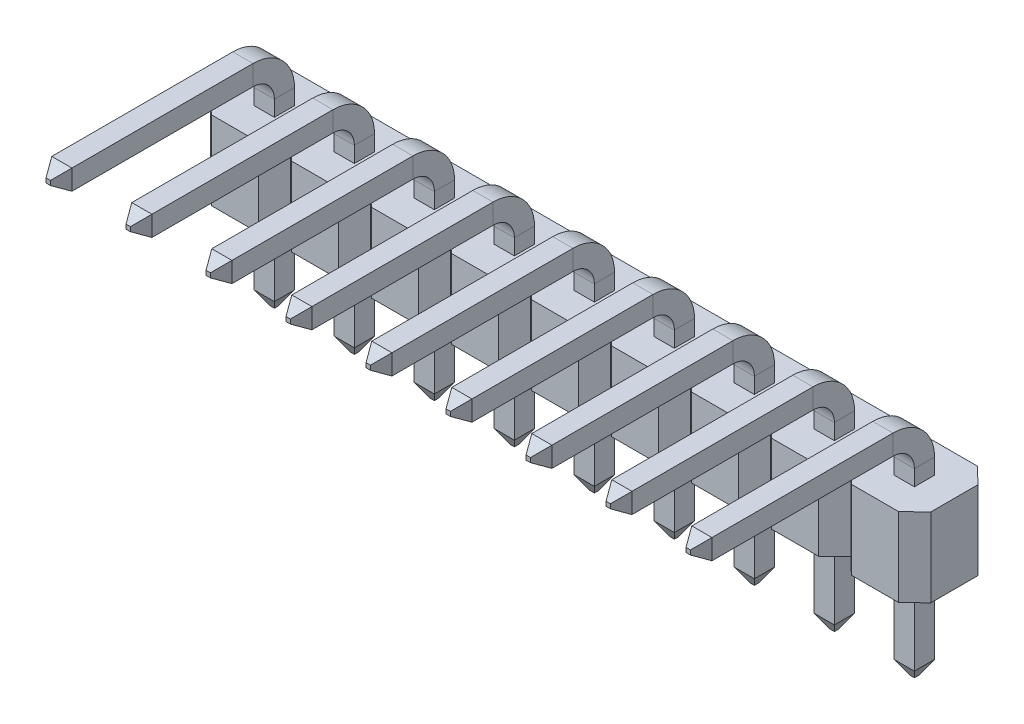
SolidWorks part; units mm, degrees
other "Plastic Body"
other "Metal Pin"
material "ABS"
ref_plane "Front Plane" through (0, 0, 0) normal (0, 0, 1) x (1, 0, 0)
ref_plane "Top Plane" through (0, 0, 0) normal (0, 1, 0) x (1, 0, 0)
ref_plane "Right Plane" through (0, 0, 0) normal (1, 0, 0) x (0, 0, -1)
sketch "Sketch1" plane through (0, 0, 0) normal (0, 1, 0) x (1, 0, 0)
  line L0 (0, 1.25) -> (0, -1.25) construction
  line L1 (-1.27, 1.25) -> (1.27, 1.25)
  line L2 (-1.27, 1.25) -> (-1.27, -1.25)
  line L3 (-1.27, -1.25) -> (1.27, -1.25)
  line L4 (1.27, 1.25) -> (1.27, -1.25)
  line L6 (-0.32, 0.32) -> (0.32, 0.32)
  line L7 (-0.32, 0.32) -> (-0.32, -0.32)
  line L8 (-0.32, -0.32) -> (0.32, -0.32)
  line L9 (0.32, 0.32) -> (0.32, -0.32)
  line L10 (-0.32, 0.32) -> (0.32, -0.32) construction
  line L11 (-0.32, -0.32) -> (0.32, 0.32) construction
  point P7 (0, 0)
  dimension "D1" = 2.5
  dimension "D2" = 2.54
  dimension "D3" = 0.64
extrude "Plastic Connection Body" add sketch "Sketch1" along normal blind 2.5
sketch "Sketch3" plane through (0, 2.5, 0) normal (0, 1, 0) x (1, 0, 0)
  line L5 (0, 1.25) -> (0, -1.25) construction
  line L6 (1.27, 1.25) -> (-1.27, 1.25) construction
  line L7 (-1.27, 0) -> (1.27, 0) construction
  line L8 (-1.27, 1.25) -> (-1.27, -1.25) construction
  line L9 (-0.75, 1.25) -> (0.75, 1.25) construction
  line L10 (-0.75, -1.25) -> (0.75, -1.25) construction
  line L11 (-1.27, 0.75) -> (-1.27, -0.75) construction
  line L12 (1.27, 0.75) -> (1.27, -0.75) construction
  line L13 (-0.75, 1.25) -> (-1.27, 0.75)
  line L14 (-1.27, 0.75) -> (-1.27, 1.25)
  line L15 (-1.27, 1.25) -> (-0.75, 1.25)
  line L16 (0.75, 1.25) -> (1.27, 0.75)
  line L17 (1.27, 0.75) -> (1.27, 1.25)
  line L18 (1.27, 1.25) -> (0.75, 1.25)
  line L19 (-1.27, -0.75) -> (-1.27, -1.25)
  line L20 (-1.27, -1.25) -> (-0.75, -1.25)
  line L21 (-0.75, -1.25) -> (-1.27, -0.75)
  line L22 (0.75, -1.25) -> (1.27, -0.75)
  line L23 (1.27, -0.75) -> (1.27, -1.25)
  line L24 (1.27, -1.25) -> (0.75, -1.25)
  dimension "D1" = 1.5
extrude "Corners Trimmed" cut sketch "Sketch3" against normal up to surface (2.5 mm away) up to face at (0, 0, 0)
sketch "Sketch4" plane through (0, 0, 0) normal (0, -1, 0) x (1, 0, 0)
  line L0 (-0.32, -0.32) -> (-0.32, 0.32) construction
  line L1 (-0.32, 0.32) -> (0.32, 0.32) construction
  line L2 (0.32, 0.32) -> (0.32, -0.32) construction
  line L3 (0.32, -0.32) -> (-0.32, -0.32) construction
  line L4 (-0.32, -0.32) -> (-0.32, 0.32)
  line L5 (-0.32, 0.32) -> (0.32, 0.32)
  line L6 (0.32, 0.32) -> (0.32, -0.32)
  line L7 (0.32, -0.32) -> (-0.32, -0.32)
sketch "Sketch5" plane through (0, 0, 0) normal (1, 0, 0) x (0, 0, -1)
  line L0 (0, 3) -> (0, -3)
  line L1 (-1, 4) -> (-7.18, 4)
  arc A0 (0, 3) -> (-1, 4) centre (-1, 3) ccw
  dimension "D4" = 1
  dimension "D1" = 3
  dimension "D2" = 7
  dimension "D3" = 7.18
sweep "Sweep-1 Bent Pin" add profiles "Sketch4" path "Sketch5"
chamfer "Bent Pin Chamfer-1" distance 0.25 angle 60 4 edges at (0.32, 4, 7.18) (0, 3.68, 7.18) (-0.32, 4, 7.18) (0, 4.32, 7.18)
chamfer "Bent Pin Chamfer-2" distance 0.25 angle 60 4 edges at (-0.32, -3, 0) (0, -3, 0.32) (0.32, -3, 0) (0, -3, -0.32)
sketch "Sketch6" plane through (0, 0, 0) normal (0, -1, 0) x (1, 0, 0)
  circle A0 centre (0, 0) radius 0.5
  dimension "D1" = 1
extrude "Cut-Extrude1" cut sketch "Sketch6" against normal blind 0.1
pattern_linear "LPattern-1" count 5 spacing 2.54 along (1, 0, 0) count 5 spacing 2.54 along (-1, 0, 0) of bodies 248 198 102
